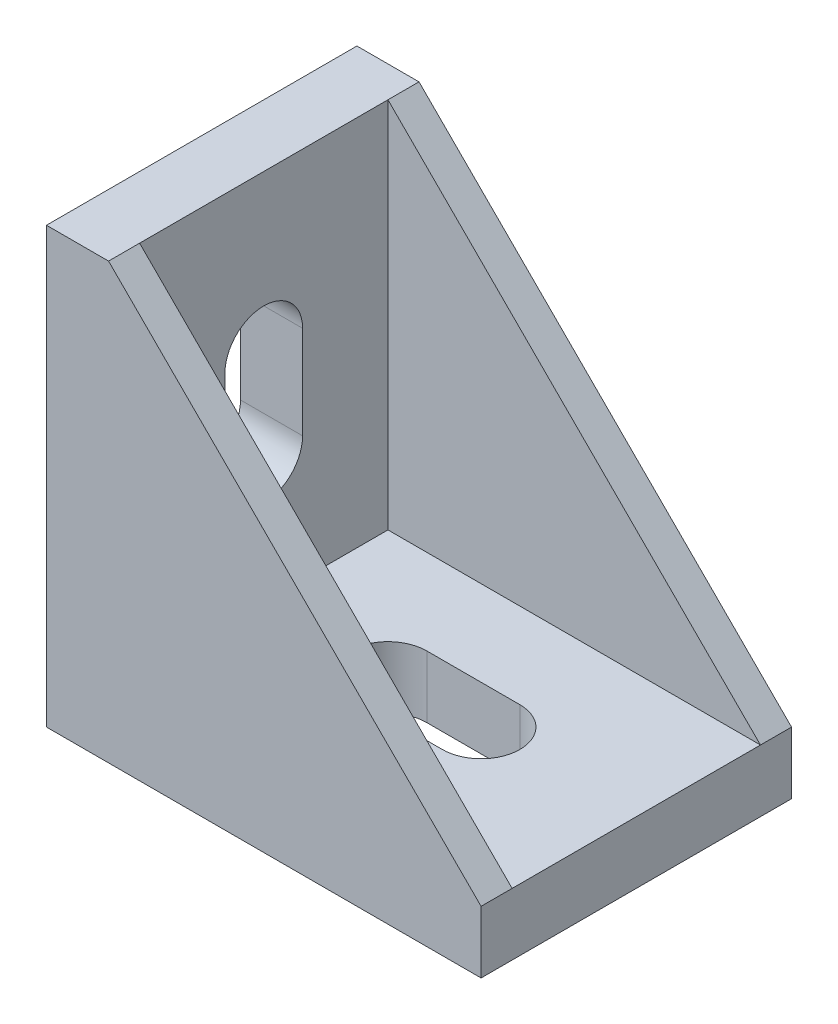
SolidWorks part; units mm, degrees
material "Алюминиевый сплав"
ref_plane "Спереди" through (0, 0, 0) normal (0, 0, 1) x (1, 0, 0)
ref_plane "Сверху" through (0, 0, 0) normal (0, 1, 0) x (1, 0, 0)
ref_plane "Справа" through (0, 0, 0) normal (1, 0, 0) x (0, 0, -1)
sketch "Эскиз1" plane through (0, 0, 0) normal (0, 0, 1) x (1, 0, 0)
  line L0 (0, 28) -> (0, 0)
  line L1 (0, 0) -> (28, 0)
  line L2 (28, 0) -> (28, 4)
  line L4 (4, 28) -> (0, 28)
  line L5 (4, 28) -> (4, 4)
  line L6 (4, 4) -> (28, 4)
  dimension "D1" = 28
  dimension "D2" = 4
extrude "Бобышка-Вытянуть1" add sketch "Эскиз1" along normal mid plane 20
sketch "Эскиз2" plane through (0, 0, 10) normal (0, 0, 1) x (1, 0, 0)
  line L0 (4, 28) -> (28, 4)
  line L1 (28, 4) -> (4, 4)
  line L2 (4, 4) -> (4, 28)
extrude "Бобышка-Вытянуть2" add sketch "Эскиз2" against normal blind 2
mirror "Зеркальное отражение2" about plane through (0, 0, 0) normal (0, 0, 1) of "Бобышка-Вытянуть2"
sketch "Эскиз3" plane through (0, 4, 0) normal (0, 1, 0) x (1, 0, 0)
  line L0 (12, 0) -> (18, 0) construction
  line L1 (12, 2.5) -> (18, 2.5)
  line L2 (12, -2.5) -> (18, -2.5)
  line L3 (0, -10) -> (0, 10) construction
  arc A0 (12, 2.5) -> (12, -2.5) centre (12, 0) ccw
  arc A1 (18, -2.5) -> (18, 2.5) centre (18, 0) ccw
  point P2 (15, 0)
  dimension "D2" = 2.5
  dimension "D3" = 12
  dimension "D1" = 6
extrude "Вырез-Вытянуть1" cut sketch "Эскиз3" against normal through all
sketch "Эскиз4" plane through (0, 0, 0) normal (0, -1, 0) x (1, 0, 0)
  line L0 (0, 10) -> (0, -10) construction
  line L1 (3, -3) -> (5.5, -3)
  line L2 (3, -3) -> (3, 3)
  line L3 (3, 3) -> (5.5, 3)
  line L4 (5.5, -3) -> (5.5, 3)
  line L5 (3, -3) -> (5.5, 3) construction
  line L6 (3, 3) -> (5.5, -3) construction
  line L7 (22.5, -3) -> (25, -3)
  line L8 (22.5, -3) -> (22.5, 3)
  line L9 (22.5, 3) -> (25, 3)
  line L10 (25, -3) -> (25, 3)
  line L11 (22.5, -3) -> (25, 3) construction
  line L12 (22.5, 3) -> (25, -3) construction
  line L13 (28, 10) -> (28, -10) construction
  point P0 (4.25, 0)
  point P5 (23.75, 0)
  dimension "D1" = 3
  dimension "D2" = 2.5
  dimension "D3" = 6
  dimension "D4" = 3
extrude "Бобышка-Вытянуть3" add sketch "Эскиз4" along normal blind 2.5
ref_plane "Плоскость1" through (0, 0, 0) normal (-0.7071, 0.7071, 0) x (0.7071, 0.7071, 0)
mirror "Зеркальное отражение3" about plane through (0, 0, 0) normal (-0.7071, 0.7071, 0) of "Бобышка-Вытянуть3", "Вырез-Вытянуть1"
